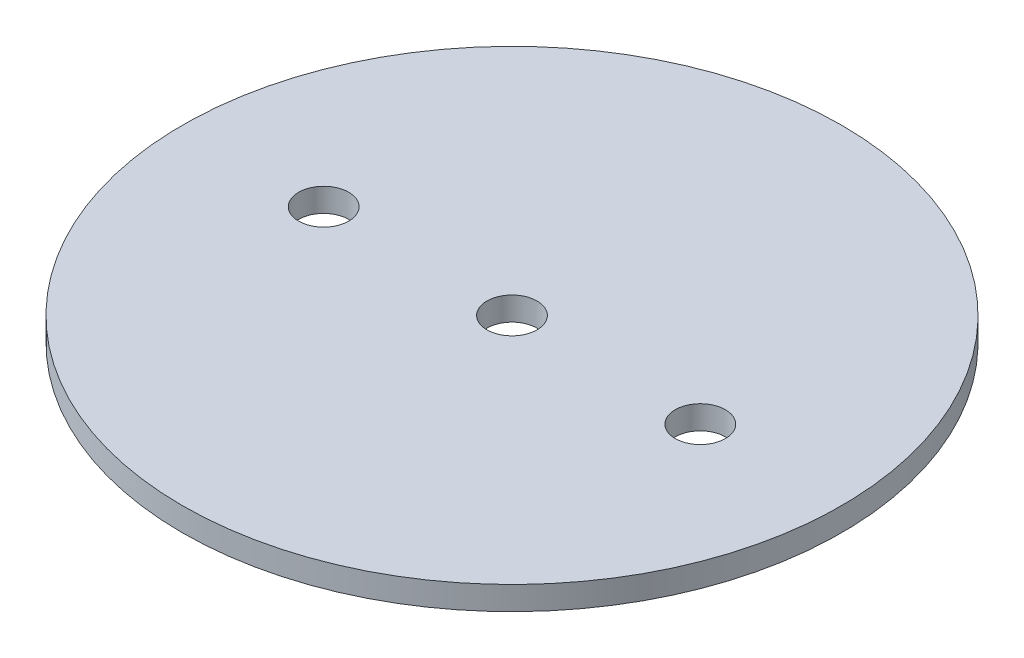
SolidWorks part; units mm, degrees
ref_plane "Front Plane" through (0, 0, 0) normal (0, 0, 1) x (1, 0, 0)
ref_plane "Top Plane" through (0, 0, 0) normal (0, 1, 0) x (1, 0, 0)
ref_plane "Right Plane" through (0, 0, 0) normal (1, 0, 0) x (0, 0, -1)
sketch "Sketch1" plane through (0, 0, 0) normal (0, 1, 0) x (1, 0, 0)
  circle A0 centre (0, 0) radius 44.45
  dimension "D1" = 88.9
extrude "Boss-Extrude1" add sketch "Sketch1" along normal mid plane 3.175
sketch "Sketch2" plane through (0, 1.5875, 0) normal (0, 1, 0) x (1, 0, 0)
  line L0 (-25.4, 0) -> (25.4, 0) construction
  point P0 (-25.4, 0)
  point P1 (25.4, 0)
  point P7 (0, 0)
  point P10 (-25.4, 0)
  point P12 (25.4, 0)
  dimension "D1" = 25.4
hole_wizard "1/4 Clearance Hole1" positions "Sketch2" profile "Sketch3" hole size "1/4" standard "ANSI Inch"
sketch "Sketch3" plane through (25.4, 1.5875, 0) normal (1, 0, 0) x (0, 0, 1)
  line L0 (0, 0) -> (0, 50.8)
  line L1 (0, 50.8) -> (3.3782, 48.7702)
  line L2 (3.3782, 48.7702) -> (3.3782, 0)
  line L5 (3.3782, 0) -> (0, 0)
  line L10 (0, 50.8) -> (-3.3782, 48.7702) construction
  line L11 (0, -6.35) -> (0, 107.95) construction
  dimension "Hole Dia." = 6.7564
  dimension "Hole Depth" = 50.8
  dimension "Drill Angle" = 118
